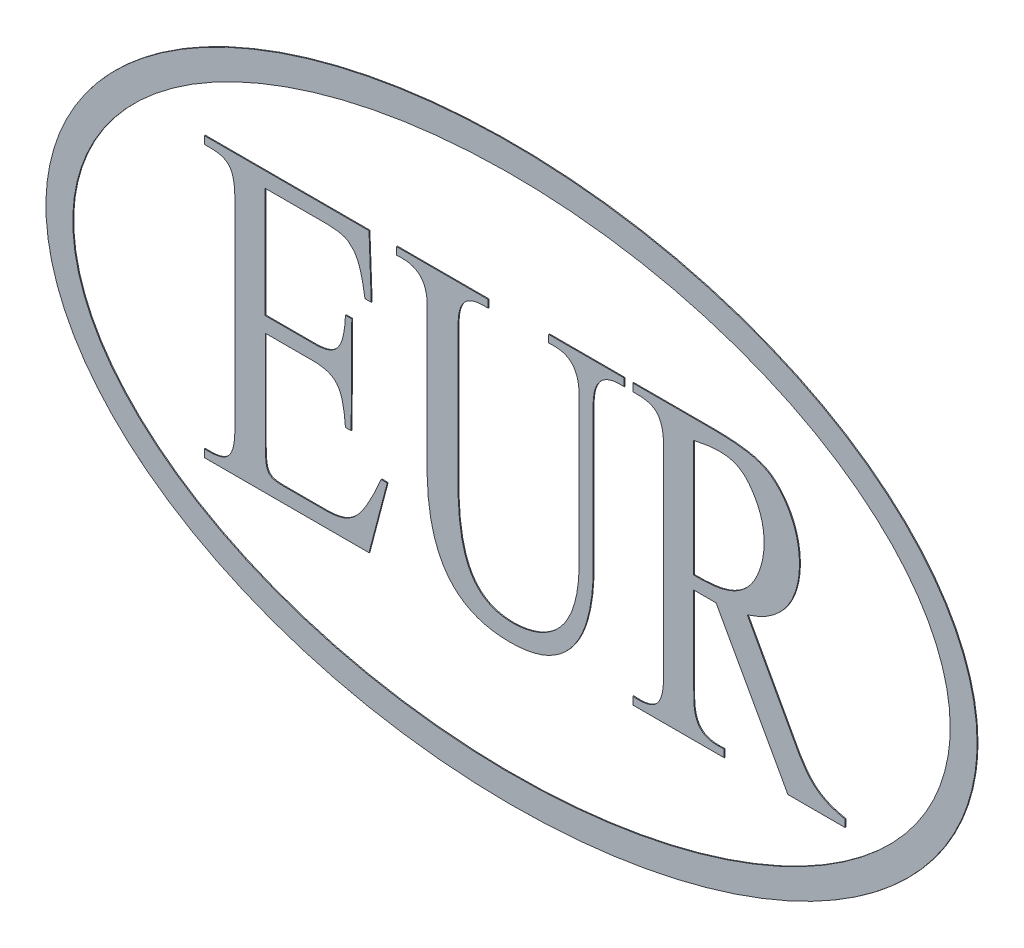
SolidWorks part; units mm, degrees
ref_plane "front" through (0, 0, 0) normal (0, 0, 1) x (1, 0, 0)
ref_plane "top" through (0, 0, 0) normal (0, 1, 0) x (1, 0, 0)
ref_plane "right" through (0, 0, 0) normal (1, 0, 0) x (0, 0, -1)
sketch "Sketch2" plane through (0, 0, 0) normal (0, 0, 1) x (1, 0, 0)
  line L0 (-16.3651, 8.7957) -> (-15.662, 8.7957)
  line L1 (-18.5443, 6.102) -> (-17.8415, 6.102)
  line L2 (-18.5443, -4.7539) -> (-17.909, -4.7539)
  line L3 (-30.8998, 11.325) -> (-30.8998, -11.0991)
  line L4 (-20.5332, -13.8852) -> (-25.4228, -13.8852)
  line L5 (7.5452, -4.7539) -> (7.5452, 11.325)
  line L6 (9.1221, -4.7539) -> (9.1221, 11.325)
  line L7 (16.9975, -10.7296) -> (16.9975, 11.0445)
  line L8 (-14.5687, -7.7901) -> (-13.8771, -7.7901)
  line L9 (37.259, -14.7391) -> (37.259, -15.5508)
  line L10 (20.3521, -10.7296) -> (20.3521, -1.0235)
  line L11 (20.3521, 0.4184) -> (20.3521, 13.4449)
  line L12 (26.3322, -0.4363) -> (32.1597, -11.0991)
  line L17 (-34.2936, 15.5979) -> (-15.9145, 15.5979)
  line L18 (-15.9145, 15.5979) -> (-15.662, 8.7957)
  line L20 (-20.5332, 13.8965) -> (-27.5454, 13.8965)
  line L21 (-27.5454, 13.8965) -> (-27.5454, 1.5862)
  line L22 (-27.5454, 1.5862) -> (-21.8469, 1.5862)
  line L24 (-17.8415, 6.102) -> (-17.909, -4.7539)
  line L26 (-21.8469, -0.1123) -> (-27.4985, -0.1123)
  line L27 (-27.4985, -0.1123) -> (-27.4985, -11.0991)
  line L28 (-13.8771, -7.7901) -> (-15.9145, -15.5508)
  line L29 (-15.9145, -15.5508) -> (-34.2936, -15.5508)
  line L30 (-34.2936, -15.5508) -> (-34.2936, -14.7001)
  line L32 (-34.2936, 14.7472) -> (-34.2936, 15.5979)
  line L33 (-12.8493, 15.5979) -> (-2.6125, 15.5979)
  line L34 (-2.6125, 15.5979) -> (-2.6125, 14.7472)
  line L36 (-5.9852, 11.325) -> (-5.9852, -4.7539)
  line L39 (4.1487, 14.7472) -> (4.1487, 15.5979)
  line L40 (4.1487, 15.5979) -> (12.5867, 15.5979)
  line L41 (12.5867, 15.5979) -> (12.5867, 14.7472)
  line L45 (-9.4227, -4.7539) -> (-9.4227, 11.325)
  line L47 (-12.8493, 14.7472) -> (-12.8493, 15.5979)
  line L48 (13.5436, 15.5979) -> (22.6411, 15.5979)
  line L52 (37.259, -15.5508) -> (30.8716, -15.5508)
  line L53 (30.8716, -15.5508) -> (22.8516, -1.0235)
  line L54 (22.8516, -1.0235) -> (20.3521, -1.0235)
  line L56 (23.7584, -14.7001) -> (23.7584, -15.5508)
  line L57 (23.7584, -15.5508) -> (13.5436, -15.5508)
  line L58 (13.5436, -15.5508) -> (13.5436, -14.7001)
  line L60 (13.5436, 14.7472) -> (13.5436, 15.5979)
  spline S0 degree 3 poles (-20.5332, 13.8965) (-18.2943, 13.8396) (-18.157, 13.2759) (-17.5502, 12.8125) (-16.9736, 11.8833) (-16.5959, 10.2409) (-16.3651, 8.7957) knots 0 0 0 0 0.355171 0.362825 0.712586 1 1 1 1
  spline S1 degree 3 poles (-21.8469, 1.5862) (-19.45, 1.6529) (-18.7032, 2.7851) (-18.5443, 6.102) knots 0 0 0 0 1 1 1 1
  spline S2 degree 3 poles (46.4484, -11.387) (50.2758, 0) (46.4484, 11.387) (35.5506, 21.0397) (19.24, 27.49) (0, 29.755) (-19.24, 27.49) (-35.5506, 21.0397) (-46.4484, 11.387) (-50.2758, 0) (-46.4484, -11.387) (-35.5506, -21.0397) (-19.24, -27.49) (0, -29.755) (19.24, -27.49) (35.5506, -21.0397) (46.4484, -11.387) (50.2758, 0) (46.4484, 11.387) knots -1.178097 -0.785398 -0.392699 0 0.392699 0.785398 1.178097 1.570796 1.963495 2.356194 2.748894 3.141593 3.534292 3.926991 4.31969 4.712389 5.105088 5.497787 5.890486 6.283185 6.675884 7.068583 7.461283 only from (49, 0) to (49, 0)
  spline S3 degree 3 poles (-21.8469, -0.1123) (-19.5465, -0.2799) (-18.8319, -1.0394) (-18.5443, -4.7539) knots 0 0 0 0 1 1 1 1
  spline S4 degree 3 poles (51.252, -6.6868) (52.374, 0) (51.252, 6.6868) (46.9571, 15.0148) (37.0451, 23.7028) (19.9374, 30.4384) (0, 32.7808) (-19.9374, 30.4384) (-37.0451, 23.7028) (-46.9571, 15.0148) (-51.252, 6.6868) (-52.374, 0) (-51.252, -6.6868) (-46.9571, -15.0148) (-37.0451, -23.7028) (-19.9374, -30.4384) (0, -32.7808) (19.9374, -30.4384) (37.0451, -23.7028) (46.9571, -15.0148) (51.252, -6.6868) (52.374, 0) (51.252, 6.6868) knots -0.785398 -0.392699 -0.19635 0 0.19635 0.392699 0.785398 1.178097 1.570796 1.963495 2.356194 2.748894 2.945243 3.141593 3.337942 3.534292 3.926991 4.31969 4.712389 5.105088 5.497787 5.890486 6.086836 6.283185 6.479535 6.675884 7.068583 only from (52, 0) to (52, 0)
  spline S5 degree 2 poles (-12.8493, 14.7472) (-9.2723, 15.1361) (-9.4227, 11.325) knots 0 0 0 1 1 1
  spline S6 degree 3 poles (-5.9852, 11.325) (-5.9568, 13.84) (-5.1252, 14.8806) (-2.6125, 14.7472) knots 0 0 0 0 1 1 1 1
  spline S7 degree 2 poles (4.1487, 14.7472) (7.6184, 15.136) (7.5452, 11.325) knots 0 0 0 1 1 1
  spline S8 degree 2 poles (12.5867, 14.7472) (9.1507, 15.0083) (9.1221, 11.325) knots 0 0 0 1 1 1
  spline S9 degree 3 poles (-34.2936, -14.7001) (-31.9688, -14.7799) (-30.9065, -14.2835) (-30.8998, -11.0991) knots 0 0 0 0 1 1 1 1
  spline S10 degree 3 poles (-27.4985, -11.0991) (-27.4663, -13.4496) (-27.2988, -13.8807) (-25.4228, -13.8852) knots 0 0 0 0 1 1 1 1
  spline S11 degree 3 poles (-34.2936, 14.7472) (-31.7781, 14.8182) (-30.9479, 14.3735) (-30.8998, 11.325) knots 0 0 0 0 1 1 1 1
  spline S12 degree 3 poles (-5.9852, -4.7539) (-5.8053, -10.2554) (-4.4383, -14.1023) (2.727, -14.5058) (7.5912, -12.1771) (7.5452, -4.7539) knots 0 0 0 0 0.537407 0.637407 1 1 1 1
  spline S13 degree 3 poles (-9.4227, -4.7539) (-9.27, -12.325) (-5.8335, -16.4689) (6.438, -16.271) (9.0449, -10.9945) (9.1221, -4.7539) knots 0 0 0 0 0.431493 0.531493 1 1 1 1
  spline S14 degree 3 poles (-20.5332, -13.8852) (-17.9393, -13.7724) (-16.7995, -12.9785) (-14.5687, -7.7901) knots 0 0 0 0 1 1 1 1
  spline S15 degree 3 poles (13.5436, -14.7001) (16.3911, -14.9648) (16.9975, -13.6598) (16.9975, -10.7296) knots 0 0 0 0 1 1 1 1
  spline S16 degree 3 poles (20.3521, 13.4449) (24.2189, 14.3463) (26.066, 13.4261) (28.8082, 8.459) (27.2725, 0.7093) (22.8842, 0.3987) (20.3521, 0.4184) knots 0 0 0 0 0.218696 0.277567 0.554134 1 1 1 1
  spline S17 degree 3 poles (26.3322, -0.4363) (30.7892, 0.922) (33.2424, 6.9867) (31.1402, 12.5114) (27.8221, 15.3642) (25.0957, 15.5586) (22.6411, 15.5979) knots 0 0 0 0 0.396591 0.71158 0.771921 1 1 1 1
  spline S18 degree 3 poles (13.5436, 14.7472) (15.8034, 14.8093) (16.9831, 14.3969) (16.9975, 11.0445) knots 0 0 0 0 1 1 1 1
  spline S19 degree 3 poles (32.1597, -11.0991) (33.4493, -13.2649) (34.5671, -14.1869) (37.259, -14.7391) knots 0 0 0 0 1 1 1 1
  spline S20 degree 3 poles (20.3521, -10.7296) (20.231, -13.9024) (21.1667, -14.9455) (23.7584, -14.7001) knots 0 0 0 0 1 1 1 1
extrude "Boss-Extrude1" add sketch "Sketch2" along normal blind 0.1 contours S4 S2 | S14 L4 S10 L27 L26 S3 L2 L24 L1 S1 L22 L21 L20 S0 L0 L18 L17 L32 S11 L3 S9 L30 L29 L28 L8 | S20 L10 L54 L53 L52 L9 S19 L12 S17 L48 L60 S18 L7 S15 L58 L57 L56 L11 S16 | L45 S5 L47 L33 L34 S6 L36 S12 L5 S7 L39 L40 L41 S8 L6 S13
